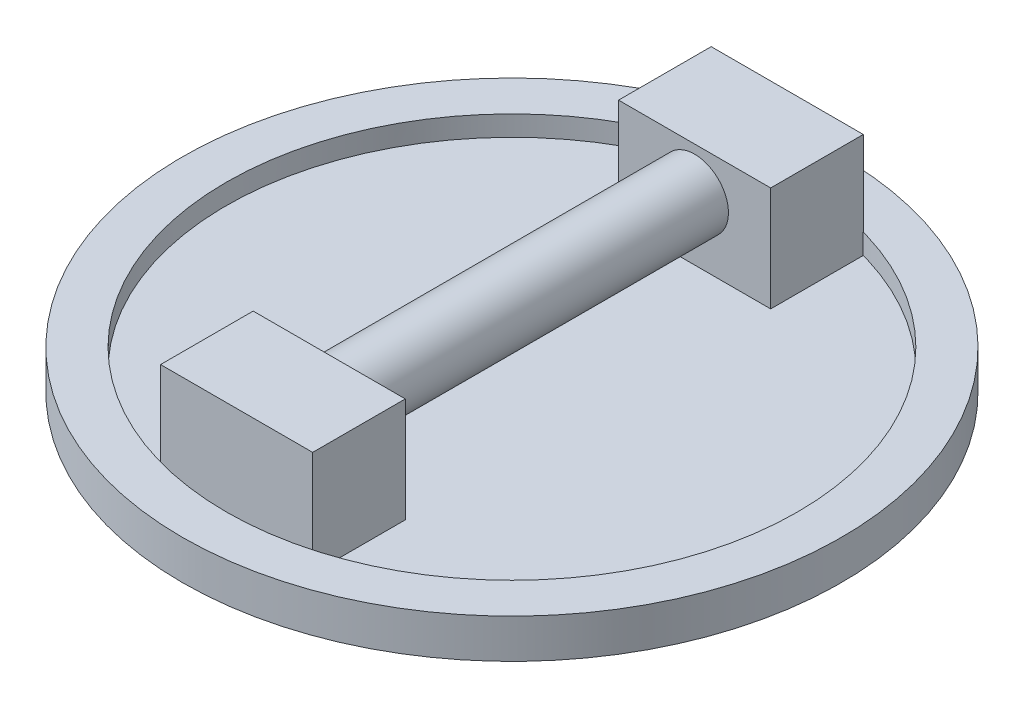
SolidWorks part; units mm, degrees
material "6061-T6 (SS)"
ref_plane "Front Plane" through (0, 0, 0) normal (0, 0, 1) x (1, 0, 0)
ref_plane "Top Plane" through (0, 0, 0) normal (0, 1, 0) x (1, 0, 0)
ref_plane "Right Plane" through (0, 0, 0) normal (1, 0, 0) x (0, 0, -1)
sketch "Sketch1" plane through (0, 0, 0) normal (0, 1, 0) x (1, 0, 0)
  circle A0 centre (0, 0) radius 123.825
  circle A1 centre (0, 0) radius 107.315
  dimension "D1" = 247.65
  dimension "D2" = 214.63
extrude "Boss-Extrude1" add sketch "Sketch1" along normal blind 14.732
sketch "Sketch2" plane through (0, 0, 0) normal (0, -1, 0) x (1, 0, 0)
  circle A0 centre (0, 0) radius 107.315
extrude "Boss-Extrude2" add sketch "Sketch2" against normal blind 7.112
sketch "Sketch3" plane through (0, 7.112, 0) normal (0, 1, 0) x (1, 0, 0)
  line L2 (-28.575, -103.4407) -> (28.575, -103.4407)
  line L3 (-28.575, -103.4407) -> (-28.575, -68.6427)
  line L4 (-28.575, -68.6427) -> (28.575, -68.6427)
  line L5 (28.575, -103.4407) -> (28.575, -68.6427)
  line L6 (-28.575, 103.4407) -> (28.575, 103.4407)
  line L7 (-28.575, 103.4407) -> (-28.575, 68.6427)
  line L8 (-28.575, 68.6427) -> (28.575, 68.6427)
  line L9 (28.575, 103.4407) -> (28.575, 68.6427)
  circle A1 centre (0, 0) radius 107.315 construction
  point P7 (0, -68.6427)
  point P15 (0, 68.6427)
  dimension "D1" = 57.15
  dimension "D2" = 34.798
  dimension "D3" = 34.798
  dimension "D4" = 57.15
extrude "Boss-Extrude9" add sketch "Sketch3" along normal blind 39.37 separate body
sketch "Sketch4" plane through (0, 0, -68.6427) normal (0, 0, 1) x (1, 0, 0)
  line L0 (-28.575, 46.482) -> (28.575, 46.482) construction
  circle A0 centre (0, 30.48) radius 12.7
  dimension "D1" = 25.4
  dimension "D2" = 16.002
extrude "Boss-Extrude10" add sketch "Sketch4" along normal up to next (137.2854 mm away)
